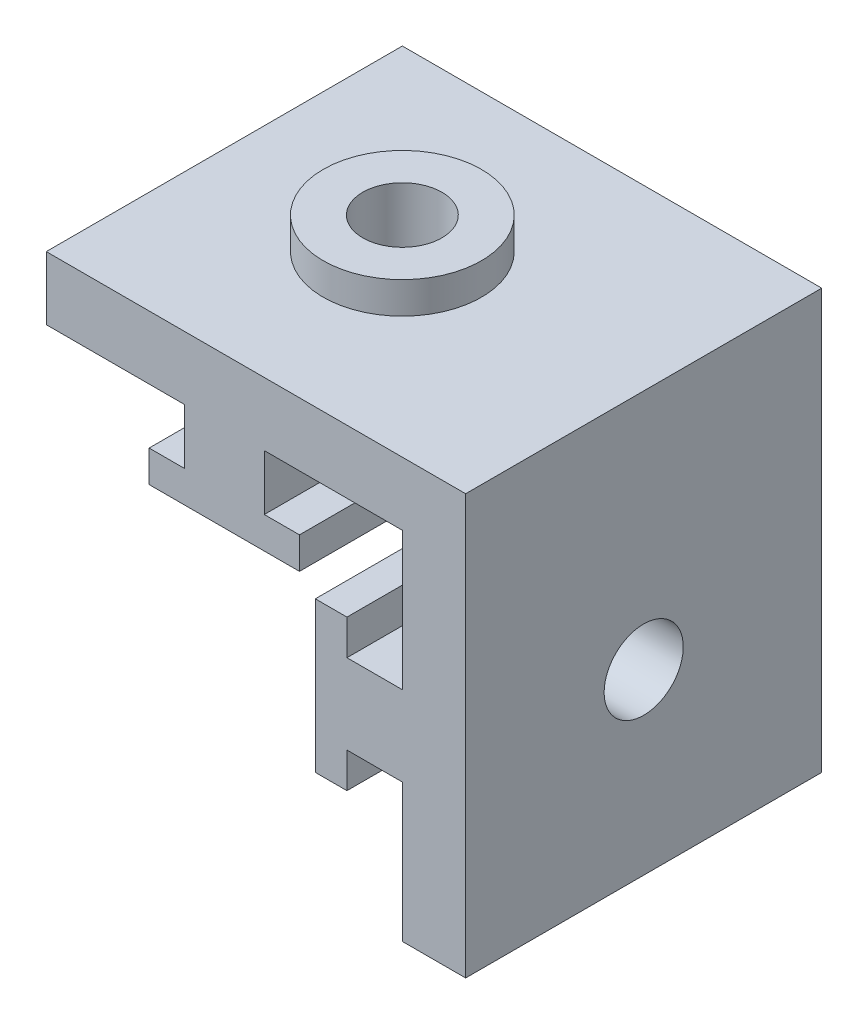
SolidWorks part; units mm, degrees
ref_plane "Plan de face" through (0, 0, 0) normal (0, 0, 1) x (1, 0, 0)
ref_plane "Plan de dessus" through (0, 0, 0) normal (0, 1, 0) x (1, 0, 0)
ref_plane "Plan de droite" through (0, 0, 0) normal (1, 0, 0) x (0, 0, -1)
sketch "Esquisse1" plane through (0, 0, 0) normal (0, 0, 1) x (1, 0, 0)
  line L0 (-53, 0) -> (0, 0)
  line L1 (0, 0) -> (0, -53)
  line L2 (0, -53) -> (-8, -53)
  line L3 (-8, -53) -> (-8, -35.5527)
  line L13 (-53, -8) -> (-53, 0)
  line L14 (-19, -30.5) -> (0, -30.5) construction
  line L15 (0, 0) -> (-26.6155, -26.6155) construction
  line L23 (-8, -8) -> (-25.4473, -8)
  line L24 (-8, -35.5527) -> (-15, -35.5527)
  line L25 (-15, -35.5527) -> (-15, -40)
  line L26 (-15, -40) -> (-19, -40)
  line L27 (-19, -40) -> (-19, -21)
  line L28 (-8, -25.4473) -> (-15, -25.4473)
  line L29 (-15, -25.4473) -> (-15, -21)
  line L30 (-15, -21) -> (-19, -21)
  line L31 (-8, -25.4473) -> (-8, -8)
  line L32 (-8, -35.5527) -> (-8, -30.5) construction
  line L33 (-8, -30.5) -> (-8, -25.4473) construction
  line L34 (-35.5527, -8) -> (-35.5527, -15)
  line L35 (-35.5527, -15) -> (-40, -15)
  line L36 (-40, -15) -> (-40, -19)
  line L37 (-40, -19) -> (-21, -19)
  line L38 (-21, -15) -> (-21, -19)
  line L39 (-25.4473, -15) -> (-21, -15)
  line L40 (-25.4473, -8) -> (-25.4473, -15)
  line L41 (-35.5527, -8) -> (-53, -8)
  line L42 (-25.4473, -8) -> (-35.5527, -8) construction
  dimension "D1" = 53
  dimension "D2" = 53
  dimension "D3" = 8
  dimension "D4" = 8
  dimension "D5" = 22.5
  dimension "D6" = 7
  dimension "D7" = 4.4473
  dimension "D8" = 4
  dimension "D9" = 9.5
extrude "Boss.-Extru.1" add sketch "Esquisse1" along normal blind 45
sketch "Esquisse2" plane through (0, 0, 0) normal (1, 0, 0) x (0, 0, -1)
  line L0 (-22.5, 0) -> (-22.5, -53) construction
  line L1 (-45, 0) -> (0, 0) construction
  line L2 (-45, -53) -> (0, -53) construction
  line L3 (-45, -30.5) -> (0, -30.5) construction
  line L6 (-45, -53) -> (-45, 0) construction
  circle A0 centre (-22.5, -30.5) radius 5
  dimension "D1" = 10
  dimension "D2" = 22.5
extrude "Enlèv. mat.-Extru.1" cut sketch "Esquisse2" against normal up to next
ref_plane "Plan1" through (0, 0, 22.5) normal (0, 0, -1) x (-1, 0, 0)
sketch "Esquisse3" plane through (0, 0, 0) normal (0, 0, -1) x (-1, 0, 0)
  line L0 (8, -8) -> (8, -25.4473) construction
  line L1 (8, -8) -> (45.3343, -8)
  line L2 (8, -8) -> (8, -44.0198)
  line L3 (8, -44.0198) -> (45.3343, -44.0198)
  line L4 (45.3343, -8) -> (45.3343, -44.0198)
  line L5 (53, -8) -> (35.5527, -8) construction
extrude "Enlèv. mat.-Extru.2" cut sketch "Esquisse3" against normal blind 20 from offset 12.5 offset against normal yes
sketch "Esquisse4" plane through (0, 0, 0) normal (0, 1, 0) x (1, 0, 0)
  line L0 (0, -22.5) -> (-53, -22.5) construction
  line L1 (0, -45) -> (0, 0) construction
  line L2 (-53, -45) -> (-53, 0) construction
  line L3 (-30.5, 0) -> (-30.5, -45) construction
  line L4 (0, 0) -> (-53, 0) construction
  line L5 (0, -45) -> (-53, -45) construction
  circle A0 centre (-30.5, -22.5) radius 10
  dimension "D2" = 20
  dimension "D1" = 22.5
extrude "Boss.-Extru.2" add sketch "Esquisse4" along normal blind 4
sketch "Esquisse5" plane through (0, 4, 0) normal (0, 1, 0) x (1, 0, 0)
  circle A0 centre (-30.5, -22.5) radius 5
  dimension "D1" = 10
extrude "Enlèv. mat.-Extru.3" cut sketch "Esquisse5" against normal up to next
